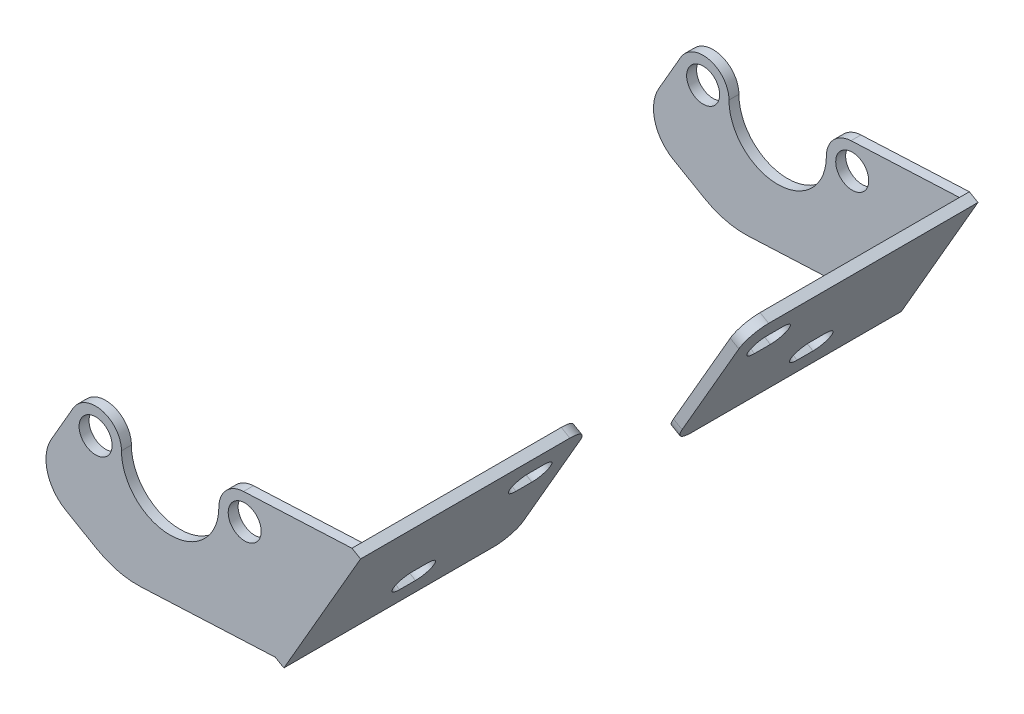
SolidWorks part; units mm, degrees
material "1023 Carbon Steel Sheet (SS)"
ref_plane "Front Plane" through (0, 0, 0) normal (0, 0, 1) x (1, 0, 0)
ref_plane "Top Plane" through (0, 0, 0) normal (0, 1, 0) x (1, 0, 0)
ref_plane "Right Plane" through (0, 0, 0) normal (1, 0, 0) x (0, 0, -1)
sketch "Sketch3" plane through (0, 0, 0) normal (0, 0, 1) x (1, 0, 0)
  line L0 (-30.949, 3.7275) -> (-44.3098, -19.4139)
  line L1 (179.172, 111.2384) -> (135.178, 136.6384) construction
  line L2 (58.0837, 9.4573) -> (23.4415, 7.8461)
  line L3 (146.2905, 155.8858) -> (16.1155, -69.5839) construction
  line L4 (-44.3098, -19.4139) -> (-16.8134, -35.2889)
  line L6 (80.347, -59.9315) -> (36.353, -34.5315) construction
  line L7 (60.8334, 7.8698) -> (36.353, -34.5315)
  line L8 (60.8334, 7.8698) -> (-13.6708, 50.8848) construction
  line L9 (60.8334, 7.8698) -> (58.0837, 9.4573)
  line L10 (36.353, -34.5315) -> (33.6033, -32.944)
  line L11 (33.6033, -32.944) -> (-16.8134, -35.2889)
  circle A0 centre (23.825, -0.4) radius 5.2705 construction
  circle A1 centre (-23.8, -0.4) radius 5.2705 construction
  circle A2 centre (23.825, -0.4) radius 5.2705
  circle A3 centre (-23.8, -0.4) radius 5.2705
  arc A4 (-14.275, -0.4) -> (-23.8, 9.125) centre (-23.8, -0.4) ccw construction
  arc A5 (23.825, 9.125) -> (14.3, -0.4) centre (23.825, -0.4) ccw construction
  arc A6 (-14.275, -0.4) -> (14.3, -0.4) centre (0.0125, -0.4) ccw construction
  arc A7 (-14.275, -0.4) -> (-23.8, 9.125) centre (-23.8, -0.4) ccw construction
  arc A8 (23.825, 9.125) -> (14.3, -0.4) centre (23.825, -0.4) ccw construction
  arc A9 (-14.275, -0.4) -> (14.3, -0.4) centre (0.0125, -0.4) ccw construction
  circle A10 centre (23.825, -0.4) radius 8.255
  arc A11 (-15.545, -0.4) -> (15.57, -0.4) centre (0.0125, -0.4) ccw
  circle A12 centre (-23.8, -0.4) radius 8.255
  arc A13 (23.825, 7.855) -> (15.57, -0.4) centre (23.825, -0.4) ccw construction
  arc A14 (-15.545, -0.4) -> (-23.8, 7.855) centre (-23.8, -0.4) ccw construction
  dimension "D2" = 90
  dimension "D3" = 31.75
  dimension "D4" = 76.2
  dimension "D5" = 3.175
  dimension "D6" = 3.175
  dimension "D1" = 1.27
extrude "Boss-Extrude1" add sketch "Sketch3" along normal up to surface (3.175 mm away)
sketch "Sketch4" plane through (0, 0, 3.175) normal (0, 0, 1) x (1, 0, 0)
  line L0 (60.8334, 7.8698) -> (36.353, -34.5315)
  line L1 (60.8334, 7.8698) -> (58.0837, 9.4573)
  line L2 (36.353, -34.5315) -> (33.6033, -32.944)
  line L3 (58.0837, 9.4573) -> (33.6033, -32.944)
  line L4 (146.2905, 155.8858) -> (16.1155, -69.5839) construction
  line L6 (58.0837, 9.4573) -> (60.8334, 7.8698) construction
  dimension "D1" = 3.175
extrude "Boss-Extrude2" add sketch "Sketch4" along normal up to surface (70.05 mm away)
fillet "Fillet1" radius 12.7 1 edges at (-44.3098, -19.4139, 1.5875)
fillet "Fillet3" radius 25.4 1 edges at (-16.8134, -35.2889, 1.5875)
sketch "Sketch5" plane through (39.4677, -22.7867, 0) normal (-0.866, 0.5, 0) x (0, 0, 1)
  line L0 (73.225, -11.7287) -> (73.225, 37.2322) construction
  line L1 (73.225, 37.2322) -> (3.175, 37.2322) construction
  line L2 (35.125, 0.9713) -> (32.585, 0.9713) construction
  line L3 (22.425, 208.1463) -> (22.425, -52.2037) construction
  line L4 (73.225, -11.7287) -> (3.175, -11.7287) construction
  line L5 (32.585, 0.9713) -> (35.125, 0.9713) construction
  line L6 (35.125, 0.9713) -> (37.665, 0.9713) construction
  line L7 (32.585, 4.9401) -> (37.665, 4.9401)
  line L8 (32.585, -2.9974) -> (37.665, -2.9974)
  line L9 (60.525, 24.5322) -> (57.985, 24.5322) construction
  line L10 (57.985, 24.5322) -> (60.525, 24.5322) construction
  line L11 (60.525, 24.5322) -> (63.065, 24.5322) construction
  line L12 (57.985, 28.5009) -> (63.065, 28.5009)
  line L13 (57.985, 20.5634) -> (63.065, 20.5634)
  circle A0 centre (60.525, 24.5322) radius 3.9687 construction
  circle A1 centre (35.125, 0.9713) radius 3.9687 construction
  circle A2 centre (32.585, 0.9713) radius 3.9687
  circle A3 centre (37.665, 0.9713) radius 3.9687
  circle A4 centre (57.985, 24.5322) radius 3.9687
  circle A5 centre (63.065, 24.5322) radius 3.9687
  dimension "D1" = 7.9375
  dimension "D2" = 12.7
  dimension "D3" = 12.7
  dimension "D4" = 12.7
  dimension "D5" = 12.7
  dimension "D6" = 2.54
  dimension "D7" = 2.54
  dimension "D8" = 2.54
  dimension "D9" = 2.54
extrude "Cut-Extrude1" cut sketch "Sketch5" against normal blind 6.35 contours A3 A2 | A2 A3 | A3 A2 | A3 L7 A2 | A3 A2 L8 | A5 A4 | A5 A4 | A5 L12 A4 | A4 A5 | A5 A4 L13
fillet "Fillet4" radius 6.35 2 edges at (59.4586, 8.6636, 73.225) (34.9781, -33.7377, 73.225)
ref_plane "Plane1" through (0, 0, 98.625) normal (0, 0, 1) x (1, 0, 0)
mirror "Mirror3" about plane through (0, 0, 98.625) normal (0, 0, 1) of bodies 106 107
